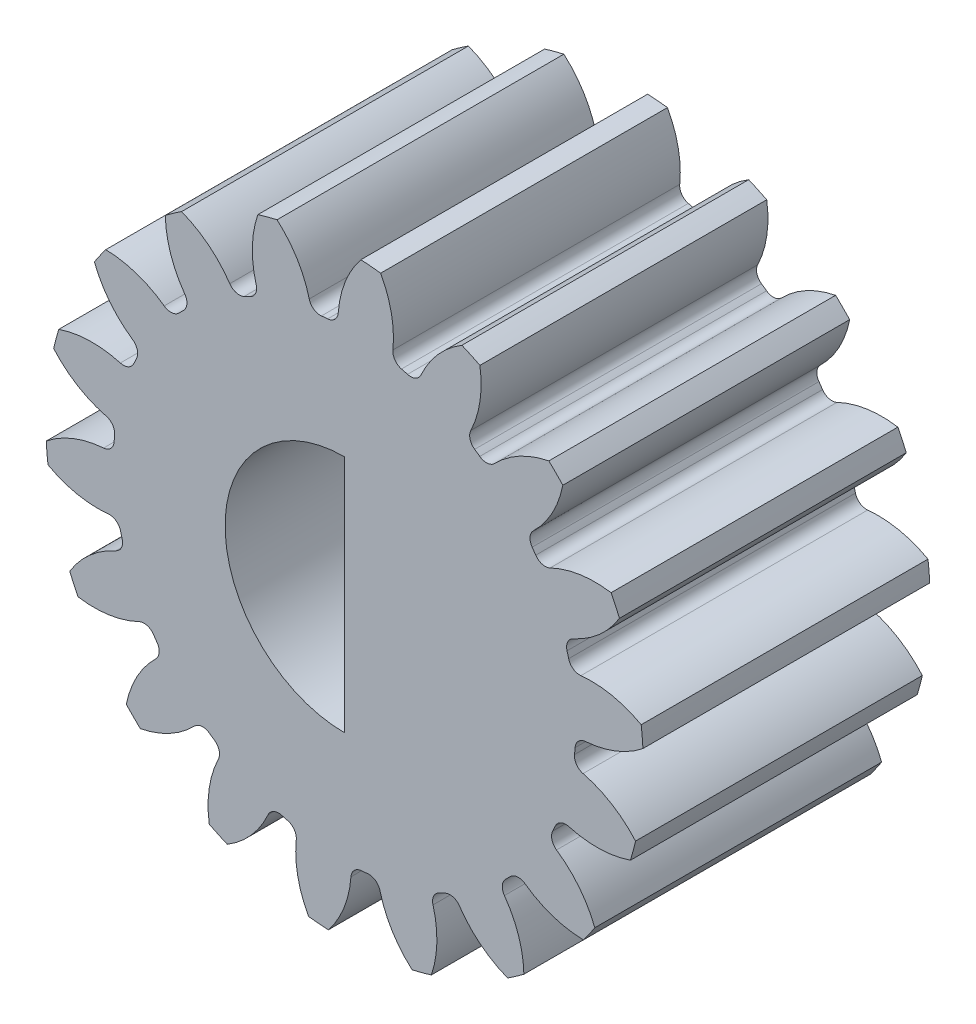
SolidWorks part; units mm, degrees
ref_plane "Front" through (0, 0, 0) normal (0, 0, 1) x (1, 0, 0)
ref_plane "Top" through (0, 0, 0) normal (0, 1, 0) x (1, 0, 0)
ref_plane "Right" through (0, 0, 0) normal (1, 0, 0) x (0, 0, -1)
sketch "Sketch3" plane through (0, 0, 0) normal (0, 0, 1) x (1, 0, 0)
  circle A0 centre (0, 0) radius 7.9375
  dimension "od" = 15.875
extrude "gearBody" add sketch "Sketch3" along normal blind 7.62
sketch "Sketch2" plane through (0, 0, 0) normal (0, 0, 1) x (1, 0, 0)
  line L0 (0, 0) -> (6.2019, 2.5689) construction
  line L1 (8.167, -2.4821) -> (0, 0) construction
  line L2 (0, 0) -> (36.3143, 0) construction
  line L3 (7.1437, -0.0161) -> (7.0369, -1.2309) construction
  line L5 (7.0903, -0.6235) -> (0, 0) construction
  line L7 (0, 0) -> (6.7129, 0) construction
  arc A0 (6.7116, -0.1347) -> (6.6321, -1.0387) centre (0, 0) ccw construction
  arc A1 (7.9261, 0.4249) -> (7.7303, -1.8017) centre (0, 0) ccw construction
  arc A2 (7.1437, -0.0161) -> (7.0369, -1.2309) centre (0, 0) ccw construction
  arc A3 (6.109, -0.6204) -> (6.1236, -0.4553) centre (0, 0) ccw
  arc A4 (8.167, -2.4821) -> (6.3363, -0.9455) centre (5.6584, -3.6119) ccw
  arc A5 (8.167, -2.4821) -> (8.4749, 1.0187) centre (0, 0) ccw
  arc A6 (8.4749, 1.0187) -> (6.4041, -0.1749) centre (6.2019, 2.5689) cw
  arc A7 (6.1236, -0.4553) -> (6.4041, -0.1749) centre (6.4264, -0.4778) cw
  arc A8 (6.3363, -0.9455) -> (6.109, -0.6204) centre (6.4112, -0.6511) cw
  point P6 (8.4749, 1.0187)
  point P22 (8.167, -2.4821)
  dimension "baseDia" = 13.4259
  dimension "od" = 15.875
  dimension "pd" = 14.2875
  dimension "rd" = 12.2809
  dimension "rFillet" = 0.3037
  dimension "pointX" = 8.4749
  dimension "pointY" = 1.0187
  dimension "CTT" = 1.2148
  dimension "flankCenterAngle" = 22.5
extrude "toothCut" cut sketch "Sketch2" along normal through all
pattern_circular "CirPattern1" count 18 over 360 about axis through (0, 0, 0) along (0, 0, 1) of "toothCut"
sketch "hub1Dia" plane through (0, 0, 0) normal (0, 0, -1) x (-1, 0, 0)
  circle A0 centre (0, 0) radius 12.7
  dimension "hub1Dia" = 25.4
sketch "hub2Dia" plane through (0, 0, 7.62) normal (0, 0, 1) x (1, 0, 0)
  circle A0 centre (0, 0) radius 12.7
  dimension "hub2dia" = 25.4
sketch "boreDia" plane through (0, 0, 0) normal (0, 0, 1) x (1, 0, 0)
  circle A0 centre (0, 0) radius 3.175
  dimension "boreDia" = 6.35
extrude "bore" cut sketch "boreDia" against normal mid plane 25400
sketch "Sketch5" plane through (0, 0, 7.62) normal (0, 0, 1) x (1, 0, 0)
  line L0 (0, 3.175) -> (0, -3.175)
  circle A0 centre (0, 0) radius 3.175 construction
  arc A1 (0, -3.175) -> (0, 3.175) centre (0, 0) ccw
extrude "Boss-Extrude1" add sketch "Sketch5" against normal blind 3.81
